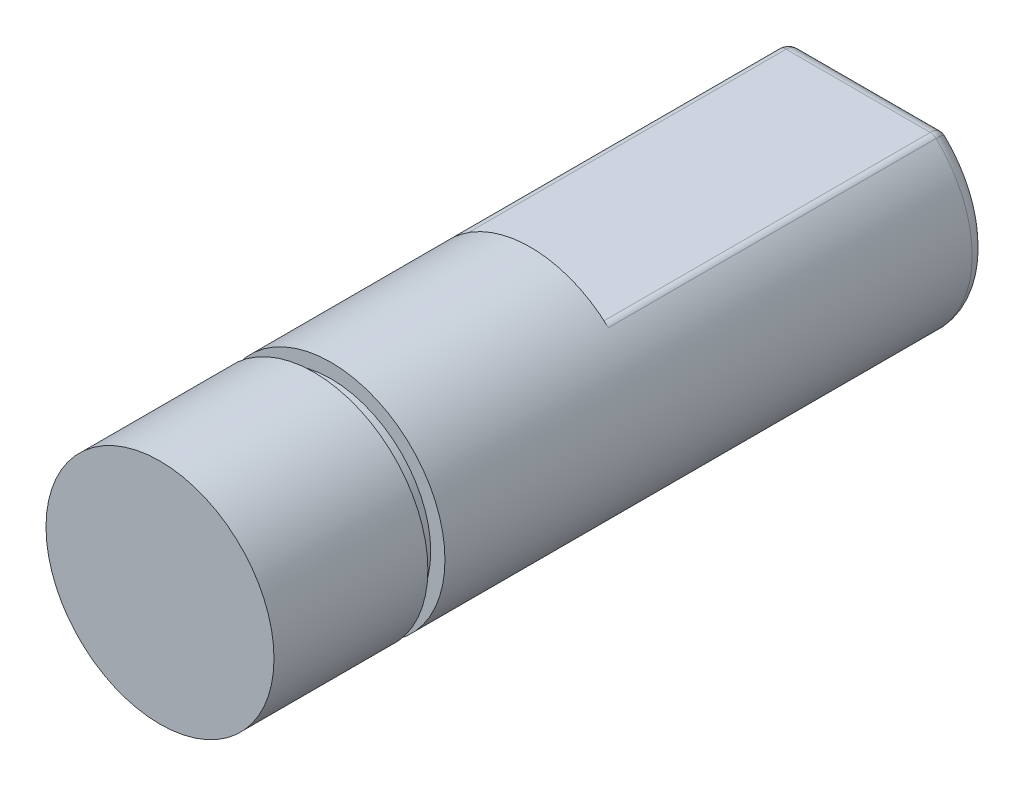
SolidWorks part; units mm, degrees
ref_plane "Front Plane" through (0, 0, 0) normal (0, 0, 1) x (1, 0, 0)
ref_plane "Top Plane" through (0, 0, 0) normal (0, 1, 0) x (1, 0, 0)
ref_plane "Right Plane" through (0, 0, 0) normal (1, 0, 0) x (0, 0, -1)
sketch "Sketch1" plane through (0, 0, 0) normal (0, 0, 1) x (1, 0, 0)
  circle A0 centre (0, 0) radius 4
  dimension "D1" = 8
extrude "Boss-Extrude1" add sketch "Sketch1" along normal blind 25
sketch "Sketch2" plane through (0, 0, 0) normal (1, 0, 0) x (0, 0, -1)
  line L1 (0, 4) -> (-12, 4)
  line L2 (0, 4) -> (0, 3)
  line L3 (0, 3) -> (-12, 3)
  line L4 (-12, 4) -> (-12, 3)
  dimension "D1" = 12
  dimension "D2" = 1
extrude "Cut-Extrude1" cut sketch "Sketch2" against normal through all and the other way through all
sketch "Sketch3" plane through (0, 0, 0) normal (1, 0, 0) x (0, 0, -1)
  line L0 (-12, 4) -> (-25, 4) construction
  line L1 (-19.6, 4) -> (-19, 4)
  line L2 (-19.6, 4) -> (-19.6, 3.5)
  line L3 (-19.6, 3.5) -> (-19, 3.5)
  line L4 (-19, 4) -> (-19, 3.5)
  line L5 (0, -4) -> (0, 3) construction
  line L6 (0, 0) -> (-36.1678, 0) construction
  dimension "D1" = 19
  dimension "D2" = 0.6
  dimension "D3" = 0.5
revolve "Cut-Revolve1" cut sketch "Sketch3" angle 360 about L6
sketch "Sketch4" plane through (0, 0, 0) normal (0, 0, -1) x (-1, 0, 0)
  circle A0 centre (0, 0) radius 1.5
  dimension "D1" = 3
extrude "Cut-Extrude2" cut sketch "Sketch4" against normal blind 3
fillet "Fillet1" radius 0.5 3 edges at (0, 3, 0) (0, -4, 0) (-1.5, 0, 0)
fillet "Fillet2" radius 0.3 4 edges at (-2.6085, 2.9022, 0.203) (2.6085, 2.9022, 0.203) (2.6458, 3, 6.25) (-2.6458, 3, 6.25)
